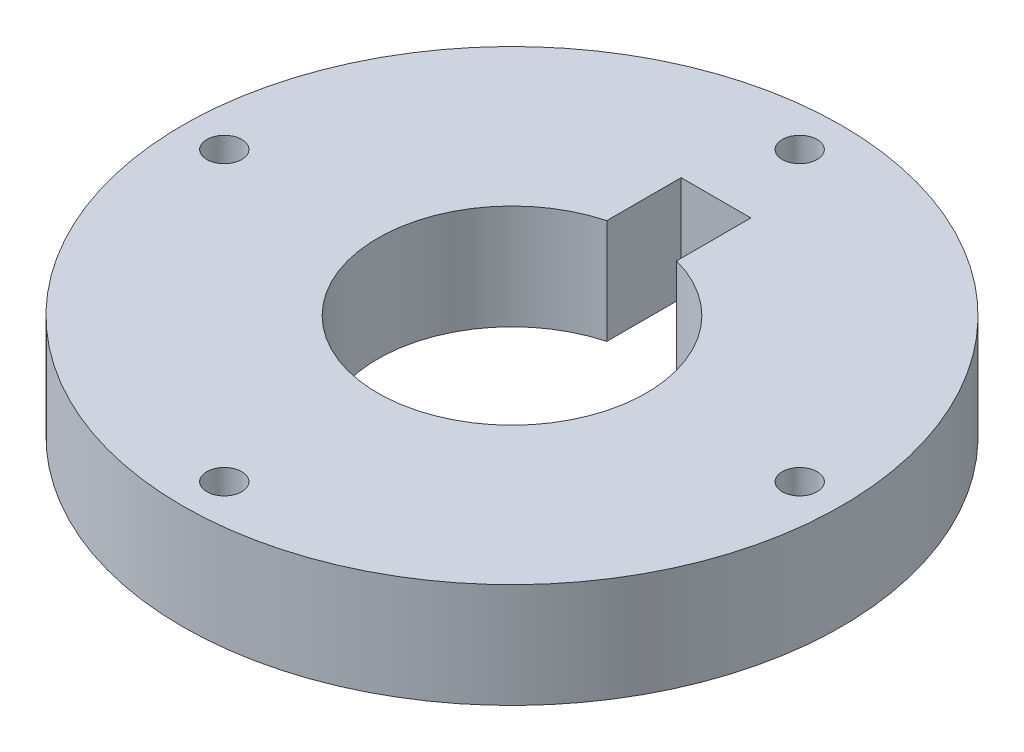
SolidWorks part; units mm, degrees
ref_plane "Front Plane" through (0, 0, 0) normal (0, 0, 1) x (1, 0, 0)
ref_plane "Top Plane" through (0, 0, 0) normal (0, 1, 0) x (1, 0, 0)
ref_plane "Right Plane" through (0, 0, 0) normal (1, 0, 0) x (0, 0, -1)
sketch "Sketch1" plane through (0, 0, 0) normal (0, 1, 0) x (1, 0, 0)
  line L0 (0, 0) -> (0, 60.4756) construction
  line L3 (-5, 18.5893) -> (-5, 29.25)
  line L4 (-5, 29.25) -> (5, 29.25)
  line L5 (5, 18.5893) -> (5, 29.25)
  circle A0 centre (0, 0) radius 47.25
  arc A1 (-5, 18.5893) -> (5, 18.5893) centre (0, 0) ccw
  circle A2 centre (0, 0) radius 41.25 construction
  circle A3 centre (0, 41.25) radius 2.5
  circle A4 centre (41.25, 0) radius 2.5
  circle A5 centre (0, -41.25) radius 2.5
  circle A6 centre (-41.25, 0) radius 2.5
  point P8 (0, 19.25)
  point P17 (0, 0)
  dimension "D1" = 94.5
  dimension "D2" = 38.5
  dimension "D3" = 82.5
  dimension "D4" = 5
  dimension "D6" = 10
  dimension "D7" = 10
  dimension "D5" = 4
extrude "Boss-Extrude1" add sketch "Sketch1" along normal blind 15
